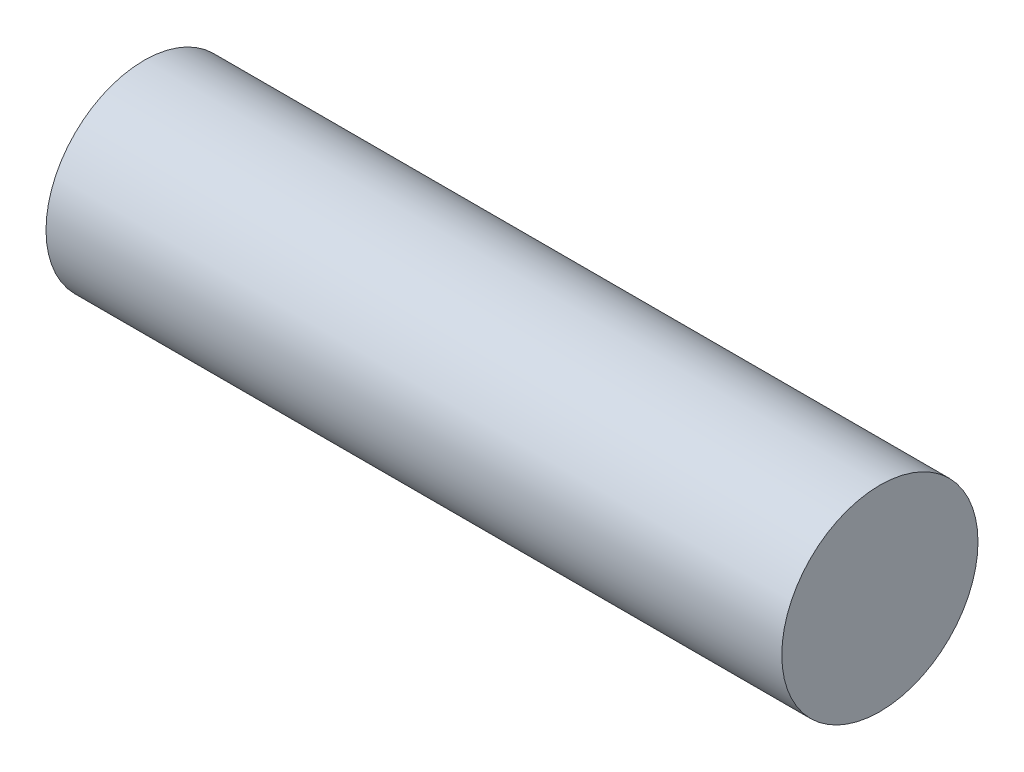
SolidWorks part; units mm, degrees
material "Ti-5Al-2.5Sn Annealed (SS)"
ref_plane "Front Plane" through (0, 0, 0) normal (0, 0, 1) x (1, 0, 0)
ref_plane "Top Plane" through (0, 0, 0) normal (0, 1, 0) x (1, 0, 0)
ref_plane "Right Plane" through (0, 0, 0) normal (1, 0, 0) x (0, 0, -1)
sketch "RivetProfile" plane through (0, 0, 0) normal (1, 0, 0) x (0, 0, -1)
  circle A0 centre (0, 0) radius 40
  dimension "D1" = 80
extrude "Boss-Extrude1" add sketch "RivetProfile" along normal blind 300 contours A0
equation "\"D1@RivetProfile\" = \"HoleMountDiameter@PrintingPress.Assembly\""
equation "\"D1@Boss-Extrude1\"= 3 * \"RivetLength@PrintingPress.Assembly\""
